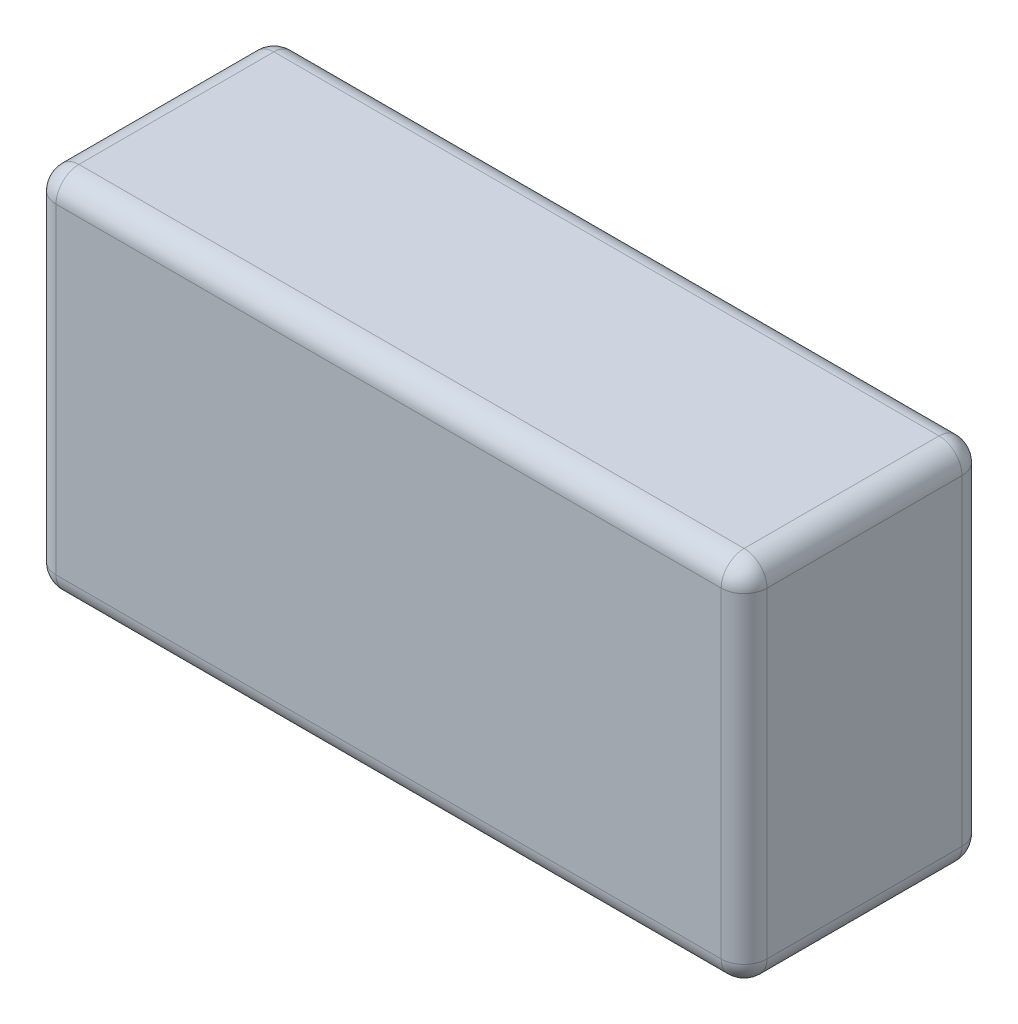
SolidWorks part; units mm, degrees
ref_plane "Plano frontal" through (0, 0, 0) normal (0, 0, 1) x (1, 0, 0)
ref_plane "Plano superior" through (0, 0, 0) normal (0, 1, 0) x (1, 0, 0)
ref_plane "Plano direito" through (0, 0, 0) normal (1, 0, 0) x (0, 0, -1)
sketch "Esboço1" plane through (0, 0, 0) normal (0, 0, 1) x (1, 0, 0)
  line L1 (-24.9147, 10.8037) -> (37.0853, 10.8037)
  line L2 (-24.9147, 10.8037) -> (-24.9147, -21.1963)
  line L3 (-24.9147, -21.1963) -> (37.0853, -21.1963)
  line L4 (37.0853, 10.8037) -> (37.0853, -21.1963)
  dimension "D1" = 62
  dimension "D2" = 32
extrude "Ressalto-extrusão1" add sketch "Esboço1" along normal blind 21
fillet "Filete1" radius 2 12 edges at (37.0853, -5.1963, 21) (37.0853, -5.1963, 0) (-24.9147, -5.1963, 21) (-24.9147, -5.1963, 0) (-24.9147, -21.1963, 10.5) (6.0853, -21.1963, 21) (37.0853, -21.1963, 10.5) (6.0853, -21.1963, 0) (37.0853, 10.8037, 10.5) (6.0853, 10.8037, 21) (-24.9147, 10.8037, 10.5) (6.0853, 10.8037, 0)
